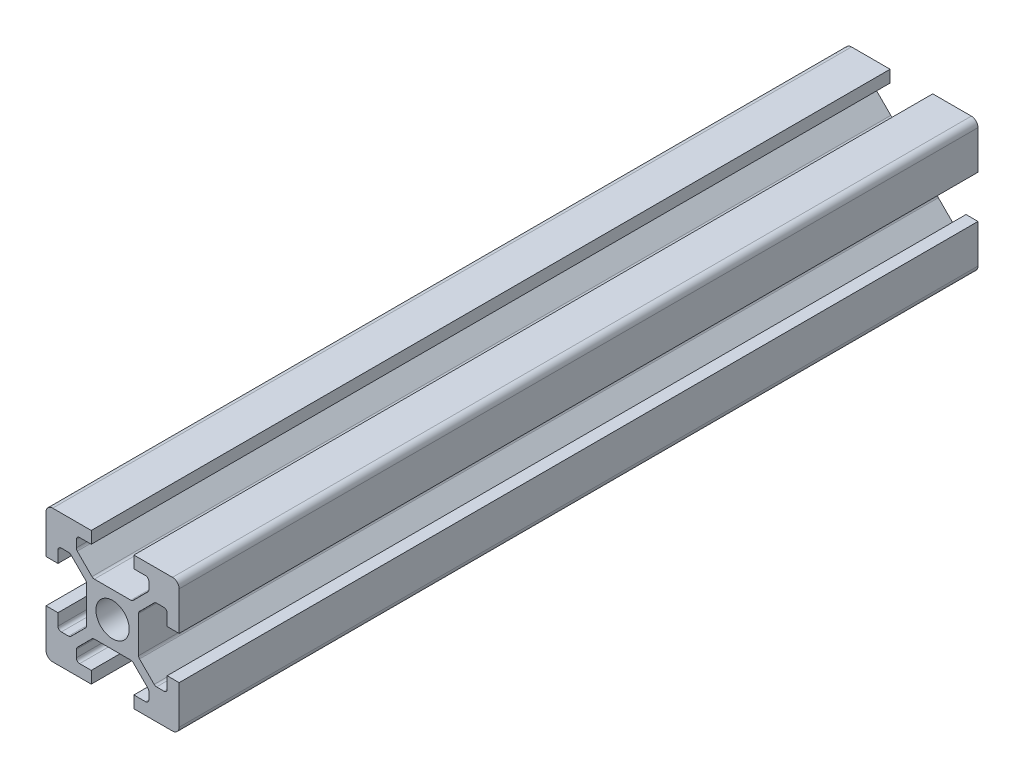
SolidWorks part; units mm, degrees
material "1060 Alloy"
ref_plane "Front Plane" through (0, 0, 0) normal (0, 0, 1) x (1, 0, 0)
ref_plane "Top Plane" through (0, 0, 0) normal (0, 1, 0) x (1, 0, 0)
ref_plane "Right Plane" through (0, 0, 0) normal (1, 0, 0) x (0, 0, -1)
sketch "Sketch1" plane through (0, 0, 0) normal (0, 0, 1) x (1, 0, 0)
  line L0 (20, 0) -> (-8.059, 28.059) construction
  line L1 (0, 0) -> (6.8, 0)
  line L2 (0, 0) -> (0, 6.8)
  line L3 (0, 20) -> (6.8, 20)
  line L4 (20, 0) -> (20, 6.8)
  line L5 (6.8, 20) -> (6.8, 18.2)
  line L6 (20, 20) -> (8.2322, 8.2322) construction
  line L7 (12.95, 6.1) -> (7.05, 6.1)
  line L8 (13.9, 7.05) -> (13.9, 12.95)
  line L9 (12.95, 13.9) -> (7.05, 13.9)
  line L10 (6.1, 7.05) -> (6.1, 12.95)
  line L11 (13.9, 6.1) -> (6.1, 13.9) construction
  line L12 (13.9, 13.9) -> (6.1, 6.1) construction
  line L13 (4.55, 16.4) -> (7.05, 13.9)
  line L14 (13.2, 18.2) -> (13.2, 20)
  line L15 (1.8, 6.8) -> (0, 6.8)
  line L16 (0, 13.2) -> (0, 20)
  line L17 (0, 13.2) -> (1.8, 13.2)
  line L18 (10, 10) -> (10, 13.9) construction
  line L19 (16.4, 4.55) -> (13.9, 7.05)
  line L20 (4.55, 16.4) -> (4.55, 18.2)
  line L21 (4.55, 18.2) -> (6.8, 18.2)
  line L22 (13.2, 18.2) -> (15.45, 18.2)
  line L23 (15.45, 18.2) -> (15.45, 16.4)
  line L24 (15.45, 16.4) -> (12.95, 13.9)
  line L25 (16.4, 4.55) -> (18.2, 4.55)
  line L26 (18.2, 4.55) -> (18.2, 6.8)
  line L27 (20, 6.8) -> (18.2, 6.8)
  line L28 (18.2, 13.2) -> (20, 13.2)
  line L29 (18.2, 13.2) -> (18.2, 15.45)
  line L30 (18.2, 15.45) -> (16.4, 15.45)
  line L31 (16.4, 15.45) -> (13.9, 12.95)
  line L32 (1.8, 4.55) -> (3.6, 4.55)
  line L33 (3.6, 15.45) -> (6.1, 12.95)
  line L34 (3.6, 15.45) -> (1.8, 15.45)
  line L35 (1.8, 15.45) -> (1.8, 13.2)
  line L36 (0, 13.2) -> (1.8, 13.2)
  line L37 (1.8, 6.8) -> (0, 6.8)
  line L38 (3.6, 4.55) -> (6.1, 7.05)
  line L39 (1.8, 6.8) -> (1.8, 4.55)
  line L40 (15.45, 3.6) -> (12.95, 6.1)
  line L41 (4.55, 3.6) -> (7.05, 6.1)
  line L42 (4.55, 1.8) -> (4.55, 3.6)
  line L43 (6.8, 1.8) -> (4.55, 1.8)
  line L44 (6.8, 1.8) -> (6.8, 0)
  line L45 (15.45, 3.6) -> (15.45, 1.8)
  line L46 (15.45, 1.8) -> (13.2, 1.8)
  line L47 (13.2, 0) -> (13.2, 1.8)
  line L48 (13.2, 20) -> (20, 20)
  line L49 (20, 13.2) -> (20, 20)
  line L50 (13.2, 0) -> (20, 0)
  line L51 (6.1, 6.1) -> (-5.5045, -5.5045) construction
  circle A0 centre (10, 10) radius 2.5
  point P25 (10, 16.4)
  point P39 (13.2, 19.1)
  point P46 (0.9, 6.8)
  dimension "D3" = 5
  dimension "D2" = 20
  dimension "D4" = 7.8
  dimension "D5" = 7.8
  dimension "D6" = 6.8
  dimension "D7" = 6.8
  dimension "D8" = 1.8
  dimension "D9" = 10.9
  dimension "D10" = 1.8
  dimension "D11" = 10.9
  dimension "D12" = 20
extrude "Boss-Extrude1" add sketch "Sketch1" along normal blind 120 contours L47 L50 L4 L27 L26 L25 L19 L8 L31 L30 L29 L28 L49 L48 L14 L22 L23 L24 L9 L13 L20 L21 L5 L3 L16 L17 L35 L34 L33 L10 L38 L32 L39 L15 L2 L1 L44 L43 L42 L41 L7 L40 L45 L46 A0
fillet "Fillet1" radius 1 4 edges at (20, 20, 60) (20, 0, 60) (0, 0, 60) (0, 20, 60)
fillet "Fillet2" radius 0.5 6 edges at (4.55, 18.2, 60) (4.55, 16.4, 60) (7.05, 13.9, 60) (15.45, 18.2, 60) (15.45, 16.4, 60) (12.95, 13.9, 60)
fillet "Fillet3" radius 0.5 6 edges at (18.2, 15.45, 60) (16.4, 15.45, 60) (13.9, 12.95, 60) (18.2, 4.55, 60) (13.9, 7.05, 60) (16.4, 4.55, 60)
fillet "Fillet4" radius 0.5 6 edges at (1.8, 15.45, 60) (3.6, 15.45, 60) (6.1, 12.95, 60) (3.6, 4.55, 60) (1.8, 4.55, 60) (6.1, 7.05, 60)
fillet "Fillet5" radius 0.5 6 edges at (7.05, 6.1, 60) (4.55, 3.6, 60) (4.55, 1.8, 60) (15.45, 1.8, 60) (15.45, 3.6, 60) (12.95, 6.1, 60)
sketch "Sketch2" plane through (0, 13.9, 0) normal (0, 1, 0) x (1, 0, 0)
  line L0 (12.7429, -60) -> (7.2571, -60) construction
  line L1 (12.7429, -120) -> (12.7429, 0) construction
  line L2 (7.2571, 0) -> (7.2571, -120) construction
  circle A0 centre (10, -60) radius 2.5
  circle A1 centre (10, -80) radius 2.5
  circle A2 centre (10, -40) radius 2.5
  point P12 (10, -60)
  dimension "D1" = 20
  dimension "D2" = 20
  dimension "D3" = 0
extrude "Cut-Extrude1" cut sketch "Sketch2" against normal blind 8
